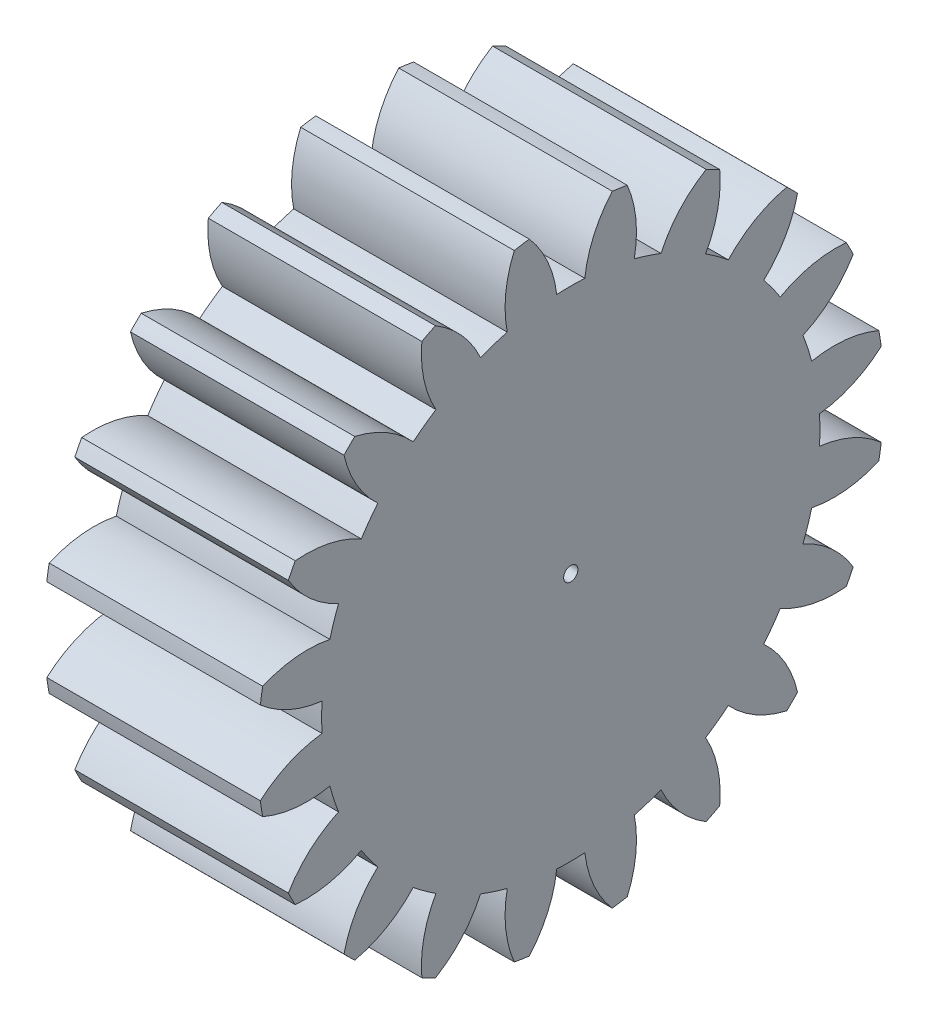
SolidWorks part; units mm, degrees
ref_plane "Plane1" through (0, 0, 0) normal (0, 0, 1) x (1, 0, 0)
ref_plane "Plane2" through (0, 0, 0) normal (0, 1, 0) x (1, 0, 0)
ref_plane "Plane3" through (0, 0, 0) normal (1, 0, 0) x (0, 0, -1)
other "Configuration Table"
sketch "HoldingSke" plane through (0, 0, 0) normal (0, 1, 0) x (1, 0, 0)
  line L0 (0, 0) -> (0.4698, -0.171)
  line L1 (-15, 0) -> (100, 0) construction
  line L2 (0, 0) -> (-2.1039, 2.3779)
  line L3 (0, 0) -> (-11.863, 4.5341)
  line L4 (0, 0) -> (8.1152, 2.9537)
  line L5 (0, 0) -> (-46.8476, -17.4728)
  line L6 (0, 0) -> (-12.4344, -8.3896)
  line L7 (-2.1039, 2.3779) -> (8.6586, 51.2059)
  line L8 (-76.2, 54.61) -> (-76.1, 54.61)
  line L9 (-71.009, 38.7566) -> (-53.1078, 45.2721)
  line L10 (-76.2, 71.12) -> (104.1128, 71.12)
  line L11 (0, 0) -> (-15, 0)
  line L12 (-76.2, 101.6) -> (-76.133, 101.6)
  line L13 (24.9733, 27.94) -> (52.9518, 28.4284)
  line L14 (24.9733, 27.94) -> (24.9743, 27.94)
  line L15 (24.9733, 27.94) -> (100.4006, 29.5858)
  line L16 (-63.627, -2) -> (-12.827, -2)
  circle A0 centre (0, 0) radius 0.5
  circle A1 centre (0, 0) radius 17.499
  circle A2 centre (0, 0) radius 37.5
  circle A3 centre (0, 0) radius 0.5
  dimension "MHD" = 34.998
  dimension "Hub_dia" = 75
  dimension "Bore" = 1
  dimension "MBD" = 1
  dimension "Num_teeth" = 20
  dimension "Pitch" = 0.5
  dimension "Overall_len" = 50
  dimension "Show_teeth" = 20
  dimension "Thickness" = 15
  dimension "OAL" = 50.0001
  dimension "T_dim" = 0.1
  dimension "Ap" = 20
  dimension "H" = 19.05
  dimension "Pitch_radius" = 180.3128
  dimension "Width" = 15
  dimension "Backlash" = 0.067
  dimension "Addendum_fac" = 1
  dimension "Dedendum_fac" = 1.25
  dimension "Clearance_fac" = 0.25
  dimension "Dedendum_add" = 0.001
  dimension "Module" = 2
sketch "BasProSke" plane through (0, 0, 0) normal (0, 1, 0) x (1, 0, 0)
  line L0 (-10, 0) -> (60, 0) construction
  line L1 (0, 0) -> (0, 22)
  line L2 (0, 0) -> (15, 0)
  line L3 (15, 0) -> (15, 22)
  line L4 (15, 22) -> (0, 22)
  dimension "Thickness" = 15
  dimension "Diameter" = 44
revolve "Base-Revolve" add sketch "BasProSke" angle 360 about L0
sketch "TooCutSke" plane through (0, 0, 0) normal (1, 0, 0) x (0, 0, -1)
  line L1 (0, 0) -> (0, 107) construction
  line L2 (0, 0) -> (-1.6864, 19.9288) construction
  line L3 (0, 0) -> (-6.2409, 39.4033) construction
  line L4 (-1.6864, 19.9288) -> (-3.1204, 19.7016) construction
  arc A0 (0.9862, 17.4712) -> (-0.9862, 17.4712) centre (0, 0) ccw
  arc A1 (2.9329, 21.8293) -> (-2.9329, 21.8293) centre (0, 0) ccw
  circle A2 centre (0, 0) radius 20 construction
  circle A3 centre (0, 0) radius 18.7939 construction
  arc A4 (-0.9862, 17.4712) -> (-2.9329, 21.8293) centre (-8.9313, 16.536) ccw
  arc A5 (2.9329, 21.8293) -> (0.9862, 17.4712) centre (8.9313, 16.536) ccw
  dimension "Root_dia" = 34.998
  dimension "Overcut_dia" = 44.0508
  dimension "Pitch_dia" = 40
  dimension "Base_dia" = 37.5877
  dimension "Flank_rad" = 8
  dimension "Half_ang" = 9
  dimension "Half_CT" = 1.4519
extrude "ToothCut" cut sketch "TooCutSke" along normal through all
fillet "Breaks" [suppressed] radius 0.04
fillet "RootFillets" [suppressed] radius 0.501
pattern_circular "TeethCuts" count 20 every 18 about axis through (-10, 0, 0) along (1, 0, 0) of "ToothCut", "RootFillets", "Breaks"
sketch "HubNeaOneSke" plane through (0, 0, 0) normal (-1, 0, 0) x (0, 0, 1)
  circle A0 centre (0, 0) radius 17.499
  dimension "Diameter" = 34.998
extrude "HubNearOne" [suppressed] add sketch "HubNeaOneSke" along normal blind 35.0001
sketch "HubNeaBotSke" plane through (0, 0, 0) normal (-1, 0, 0) x (0, 0, 1)
  circle A0 centre (0, 0) radius 17.499
  dimension "Diameter" = 34.998
extrude "HubNearBoth" [suppressed] add sketch "HubNeaBotSke" along normal blind 17.5
ref_plane "FarPln" through (15, 0, 0) normal (1, 0, 0) x (0, 0, -1)
sketch "HubFarSke" plane through (15, 0, 0) normal (1, 0, 0) x (0, 0, -1)
  circle A0 centre (0, 0) radius 17.499
  dimension "Diameter" = 34.998
extrude "HubFar" [suppressed] add sketch "HubFarSke" along normal blind 17.5
sketch "BorSke" plane through (0, 0, 0) normal (1, 0, 0) x (0, 0, -1)
  circle A0 centre (0, 0) radius 0.5
  dimension "Diameter" = 1
extrude "Bore" cut sketch "BorSke" along normal mid plane 100.0001
sketch "KeySke" plane through (0, 0, 0) normal (1, 0, 0) x (0, 0, -1)
  line L0 (-0.05, 0) -> (-0.05, 0.6)
  line L1 (-0.05, 0.6) -> (0.05, 0.6)
  line L2 (0.05, 0.6) -> (0.05, 0)
  line L3 (0, 0) -> (0, 34) construction
  line L4 (-0.05, 0) -> (0.05, 0)
  dimension "Offset" = 0.6
  dimension "Width" = 0.1
extrude "Keyway" [suppressed] cut sketch "KeySke" along normal mid plane 100.0001
pattern_circular "Keyway2" [suppressed] count 2 every 90 about axis through (-10, 0, 0) along (1, 0, 0)
equation "' \"Module@HoldingSke\" = 6.35"
equation "' \"Num_teeth@HoldingSke\" = 12"
equation "' \"Ap@HoldingSke\" =  20"
equation "' \"Ap@HoldingSke\" = 20"
equation "' \"Width@HoldingSke\" = 0.5 * 25.4"
equation "' \"Hub_dia@HoldingSke\"= 1 * 25.4"
equation "' \"Hub_dia@HoldingSke\" = 1 * 25.4"
equation "' \"Overall_len@HoldingSke\" = 1.0 * 25.4"
equation "' \"Bore@HoldingSke\" = 0.75 * 25.4"
equation "' \"T_dim@HoldingSke\" = 0.1 * 25.4"
equation "' \"Width@KeySke\" = 0.25 * 25.4"
equation "' \"Show_teeth@HoldingSke\" = 13"
equation "' \"Backlash@HoldingSke\" = 0.009 * 25.4"
equation "' \"Addendum_fac@HoldingSke\" = 1.0"
equation "' \"Dedendum_fac@HoldingSke\" = 1.25"
equation "' \"Dedendum_add@HoldingSke\" = 0.00005 * 25.4"
equation "' \"Clearance_fac@HoldingSke\" = 0.25"
equation "\"Pitch@HoldingSke\" = 1 / \"Module@HoldingSke\""
equation "\"Overcut_dia@TooCutSke\" = (\"Num_teeth@HoldingSke\" + 2 * \"Addendum_fac@HoldingSke\") / \"Pitch@HoldingSke\" + 0.002 * 25.4"
equation "\"Pitch_dia@TooCutSke\" = \"Num_teeth@HoldingSke\" / \"Pitch@HoldingSke\""
equation "\"Base_dia@TooCutSke\" = \"Num_teeth@HoldingSke\" / \"Pitch@HoldingSke\" * cos((\"Ap@HoldingSke\"  * 3.14159265 / 180))"
equation "\"Root_dia@TooCutSke\" = (\"Num_teeth@HoldingSke\" + 2) / \"Pitch@HoldingSke\" - 2 * (\"Addendum_fac@HoldingSke\" + \"Dedendum_fac@HoldingSke\") / \"Pitch@HoldingSke\" - \"Dedendum_add@HoldingSke\" * 2"
equation "\"Half_ang@TooCutSke\" = 180 / \"Num_teeth@HoldingSke\""
equation "\"Half_CT@TooCutSke\" = \"Num_teeth@HoldingSke\" / \"Pitch@HoldingSke\" * sin((3.14159265 / 2 / \"Num_teeth@HoldingSke\")) / 2 - 7 * \"Backlash@HoldingSke\" / 4"
equation "\"Flank_rad@TooCutSke\" = \"Num_teeth@HoldingSke\" / \"Pitch@HoldingSke\" / 5"
equation "\"Radius@RootFillets\" = \"Clearance_fac@HoldingSke\" / \"Pitch@HoldingSke\" + \"Dedendum_add@HoldingSke\""
equation "\"Break_rad@Breaks\" = 0.02 / \"Pitch@HoldingSke\""
equation "\"Thickness@HoldingSke\" = \"Width@HoldingSke\""
equation "\"OAL@HoldingSke\" = \"Thickness@HoldingSke\""
equation "\"MHD@HoldingSke\" = (\"Num_teeth@HoldingSke\" + 2) / \"Pitch@HoldingSke\" - 2 * (\"Addendum_fac@HoldingSke\" + \"Dedendum_fac@HoldingSke\")  / \"Pitch@HoldingSke\" - \"Dedendum_add@HoldingSke\" * 2"
equation "\"MBD@HoldingSke\" = (\"Num_teeth@HoldingSke\" + 2) / \"Pitch@HoldingSke\" - 2 * (\"Addendum_fac@HoldingSke\" + \"Dedendum_fac@HoldingSke\")  / \"Pitch@HoldingSke\" - \"Dedendum_add@HoldingSke\" * 2 - 0.002 * 25.4"
equation "\"MHD@HoldingSke\" = ((sgn( \"MHD@HoldingSke\" - \"Hub_dia@HoldingSke\" )-1)*( \"MHD@HoldingSke\" - \"Hub_dia@HoldingSke\" ))/-2+ \"Hub_dia@HoldingSke\""
equation "\"MBD@HoldingSke\" = ((sgn( \"MBD@HoldingSke\" - \"Bore@HoldingSke\" )-1)*( \"MBD@HoldingSke\" - \"Bore@HoldingSke\" ))/-2+ \"Bore@HoldingSke\""
equation "\"OAL@HoldingSke\" = ((sgn( \"OAL@HoldingSke\" - \"Overall_len@HoldingSke\" )+1)*( \"OAL@HoldingSke\" - \"Overall_len@HoldingSke\" ))/2 + \"Overall_len@HoldingSke\" + 0.000002 * 25.4"
equation "\"Num_teeth@TeethCuts\" = int( \"Show_teeth@HoldingSke\" ) + 1"
equation "\"Num_teeth@TeethCuts\" = ((sgn( \"Num_teeth@TeethCuts\" - \"Num_teeth@HoldingSke\" )-1)*( \"Num_teeth@TeethCuts\" - \"Num_teeth@HoldingSke\" ))/-2+ \"Num_teeth@HoldingSke\""
equation "\"Num_teeth@TeethCuts\" = ((sgn( \"Num_teeth@TeethCuts\" - 2.0)+1)*( \"Num_teeth@TeethCuts\" - 2.0))/2 +2.0"
equation "\"Angle@TeethCuts\" = 360.0 / \"Num_teeth@HoldingSke\""
equation "\"Diameter@BasProSke\" = (\"Num_teeth@HoldingSke\" + 2 * \"Addendum_fac@HoldingSke\") / \"Pitch@HoldingSke\""
equation "\"Thickness@BasProSke\"  = \"Thickness@HoldingSke\""
equation "' \"Fillet_rad@BasProSke\" =  \"Thickness@HoldingSke\" * 0.05"
equation "' \"Fillet_rad@BasProSke\" = \"Thickness@HoldingSke\" * 0.05"
equation "\"MHD@HoldingSke\" = ((sgn( \"MHD@HoldingSke\" - \"Root_dia@TooCutSke\" )-1)*( \"MHD@HoldingSke\" - \"Root_dia@TooCutSke\" ))/-2+ \"Root_dia@TooCutSke\""
equation "\"Diameter@HubNeaOneSke\" = \"MHD@HoldingSke\""
equation "\"Length@HubNearOne\" = \"OAL@HoldingSke\" - \"Thickness@BasProSke\""
equation "\"Diameter@HubNeaBotSke\" = \"MHD@HoldingSke\""
equation "\"Length@HubNearBoth\" = ( \"OAL@HoldingSke\" - \"Thickness@BasProSke\" ) / 2.0"
equation "\"Thickness@FarPln\" = \"Thickness@BasProSke\""
equation "\"Diameter@HubFarSke\" = \"MHD@HoldingSke\""
equation "\"Length@HubFar\" = ( \"OAL@HoldingSke\" - \"Thickness@BasProSke\" ) / 2.0"
equation "\"Diameter@BorSke\" = \"MBD@HoldingSke\""
equation "\"D1@Bore\" = \"OAL@HoldingSke\" * 2.0"
equation "\"D1@Keyway\" = \"OAL@HoldingSke\" * 2.0"
equation "\"Offset@KeySke\" = \"T_dim@HoldingSke\" + \"MBD@HoldingSke\" / 2.0"
